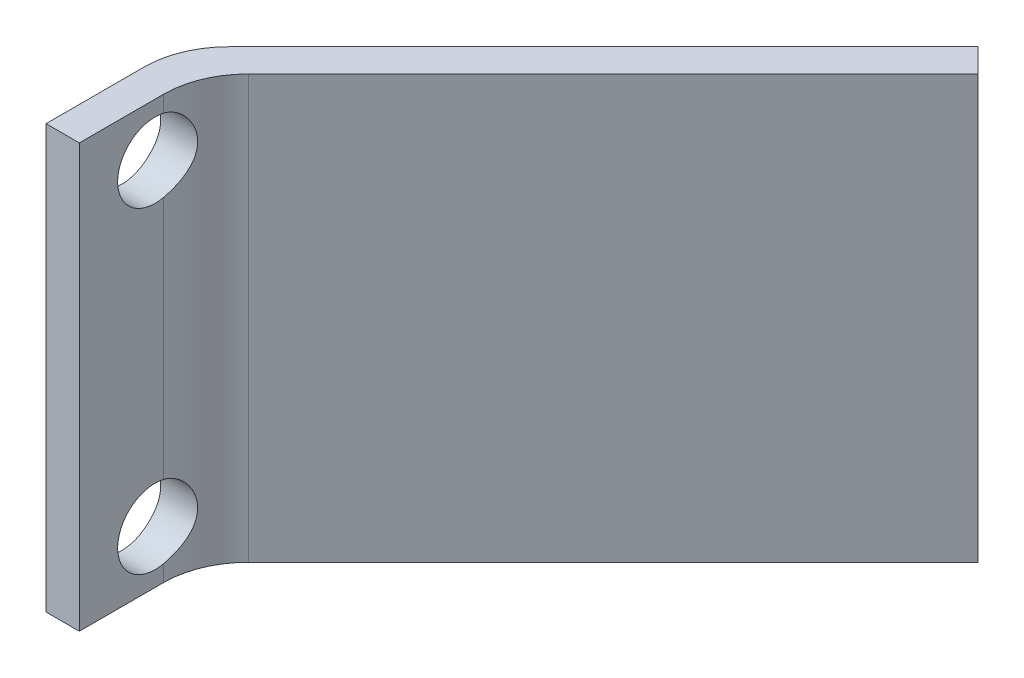
SolidWorks part; units mm, degrees
ref_plane "Front Plane" through (0, 0, 0) normal (0, 0, 1) x (1, 0, 0)
ref_plane "Top Plane" through (0, 0, 0) normal (0, 1, 0) x (1, 0, 0)
ref_plane "Right Plane" through (0, 0, 0) normal (1, 0, 0) x (0, 0, -1)
sketch "Sketch1" plane through (0, 0, 0) normal (0, 1, 0) x (1, 0, 0)
  line L0 (0, 0) -> (0, 4)
  line L1 (0, 0) -> (1, 0)
  line L2 (0, 4) -> (1, 4)
  line L3 (1, 0) -> (1, 4)
  dimension "D1" = 1
  dimension "D2" = 4
extrude "Boss-Extrude1" add sketch "Sketch1" along normal blind 12.7
sketch "Sketch2" plane through (0, 0, 0) normal (0, 1, 0) x (1, 0, 0)
  line L0 (0, 4) -> (11.9929, 15.9929)
  line L1 (0, 4) -> (0.7071, 3.2929)
  line L2 (11.9929, 15.9929) -> (12.7, 15.2858)
  line L3 (0.7071, 3.2929) -> (12.7, 15.2858)
  line L4 (1, 4) -> (0, 4) construction
  dimension "D1" = 45
  dimension "D2" = 12.7
extrude "Boss-Extrude2" add sketch "Sketch2" along normal up to surface (12.7 mm away) up to face at (0.5, 12.7, -2)
fillet "Fillet1" radius 2.54 2 edges at (0, 6.35, -4) (1, 6.35, -3.5858)
sketch "Sketch3" plane through (1, 0, 0) normal (1, 0, 0) x (0, 0, -1)
  line L0 (2.0199, 6.35) -> (2.5337, 6.35) construction
  line L1 (2.0199, 12.7) -> (2.0199, 0) construction
  line L2 (2.5337, 0) -> (2.5337, 12.7) construction
  line L3 (2.2768, 11.1125) -> (2.2768, 1.5875) construction
  circle A0 centre (2.2768, 11.1125) radius 1.125
  circle A1 centre (2.2768, 1.5875) radius 1.125
  point P8 (2.2768, 6.35)
  point P9 (2.2768, 6.35)
  dimension "D2" = 2.25
  dimension "D1" = 9.525
extrude "Cut-Extrude1" cut sketch "Sketch3" against normal through all both and the other way through all
